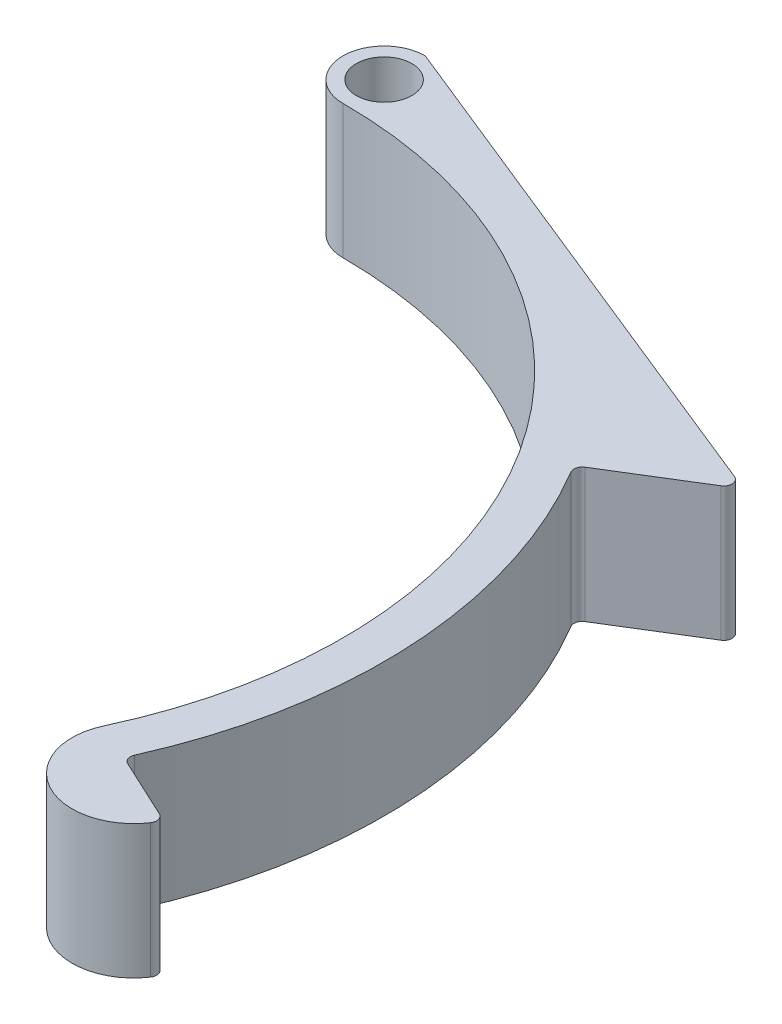
SolidWorks part; units mm, degrees
ref_plane "Front Plane" through (0, 0, 0) normal (0, 0, 1) x (1, 0, 0)
ref_plane "Top Plane" through (0, 0, 0) normal (0, 1, 0) x (1, 0, 0)
ref_plane "Right Plane" through (0, 0, 0) normal (1, 0, 0) x (0, 0, -1)
sketch "Sketch1" plane through (0, 0, 0) normal (0, 1, 0) x (1, 0, 0)
  line L0 (0, 0) -> (40.7839, -19.0178) construction
  line L1 (0, 0) -> (0, -45) construction
  line L2 (0, 0) -> (75.2171, -35.0743) construction
  line L3 (0, 53) -> (51.921, 32.0189)
  line L4 (51.921, 32.0189) -> (41.707, 25.7201)
  line L5 (0, 53) -> (0, 49)
  line L7 (0, 49) -> (0, 53)
  line L8 (51.6595, -24.0892) -> (44.4091, -20.7083)
  circle A0 centre (0, 0) radius 45 construction
  arc A1 (0, 45) -> (40.7839, -19.0178) centre (0, 0) cw
  arc A2 (0, 45) -> (0, 53) centre (0, 49) cw
  arc A4 (44.4091, -20.7083) -> (0, 49) centre (0, 0) ccw
  circle A5 centre (0, 49) radius 2.7
  arc A6 (41.707, 25.7201) -> (0, 49) centre (0, 0) ccw
  arc A7 (40.7839, -19.0178) -> (51.6595, -24.0892) centre (46.2217, -21.5535) ccw
  dimension "D1" = 90
  dimension "D5" = 56
  dimension "D6" = 5.4
  dimension "D2" = 65
  dimension "D3" = 8
  dimension "D4" = 4
  dimension "D7" = 12
  dimension "D8" = 12
extrude "Boss-Extrude1" add sketch "Sketch1" along normal blind 13
fillet "Fillet1" radius 0.8 5 edges at (0, 6.5, -53) (51.921, 6.5, -32.0189) (41.707, 6.5, -25.7201) (51.6595, 6.5, 24.0892) (44.4091, 6.5, 20.7083)
